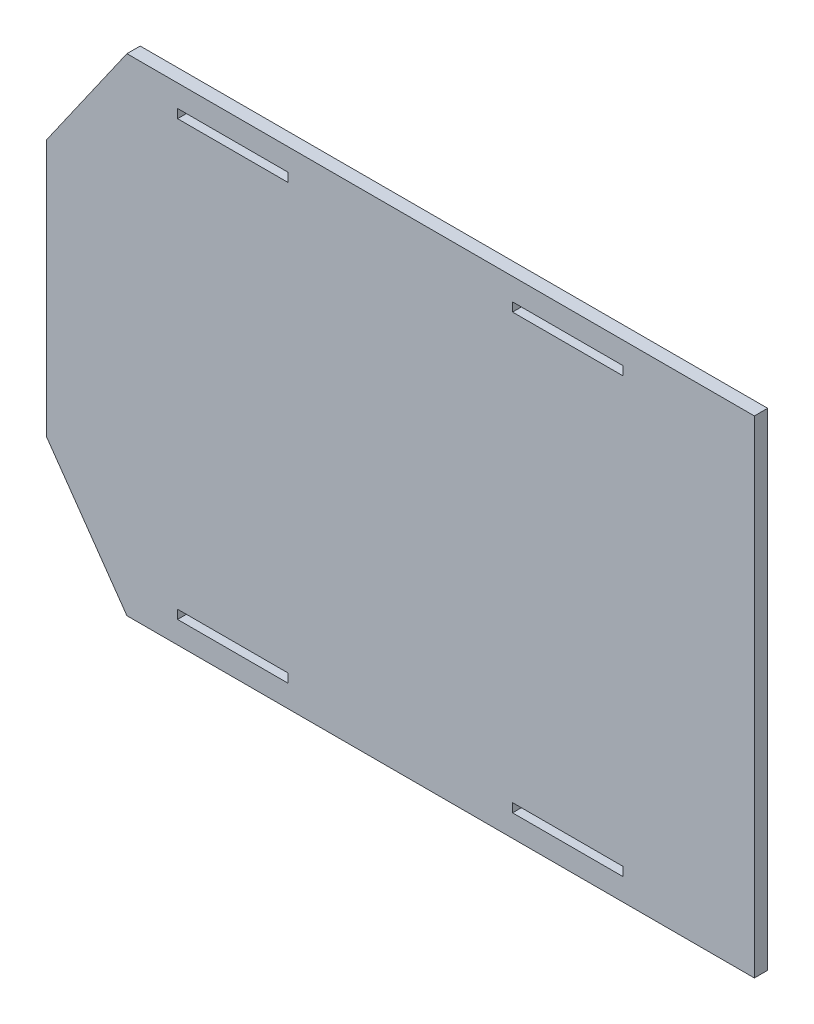
SolidWorks part; units mm, degrees
ref_plane "Ebene vorne" through (0, 0, 0) normal (0, 0, 1) x (1, 0, 0)
ref_plane "Ebene oben" through (0, 0, 0) normal (0, 1, 0) x (1, 0, 0)
ref_plane "Ebene rechts" through (0, 0, 0) normal (1, 0, 0) x (0, 0, -1)
sketch "Skizze1" plane through (0, 0, 0) normal (0, 0, 1) x (1, 0, 0)
  line L1 (0, 0) -> (320, 0)
  line L2 (0, 0) -> (0, 220)
  line L3 (0, 220) -> (320, 220)
  line L4 (320, 0) -> (320, 220)
  dimension "D1" = 220
  dimension "D2" = 320
extrude "Aufsatz-Linear austragen1" add sketch "Skizze1" along normal blind 6
sketch "Skizze2" plane through (0, 0, 6) normal (0, 0, 1) x (1, 0, 0)
  line L0 (0, 110) -> (508.8137, 110) construction
  line L1 (0, 220) -> (0, 0) construction
  line L2 (160, -38.5334) -> (160, 341.9392) construction
  line L3 (320, 0) -> (320, 220) construction
  line L4 (109.3, 206) -> (109.3, 210) construction
  line L5 (59.3, 210) -> (109.3, 210)
  line L6 (59.3, 210) -> (59.3, 206)
  line L7 (59.3, 206) -> (109.3, 206)
  line L8 (109.3, 210) -> (109.3, 206)
  dimension "D1" = 50
  dimension "D2" = 4
  dimension "D4" = 96
extrude "Schnitt-Linear austragen1" cut sketch "Skizze2" against normal up to next (6 mm away)
ref_plane "Ebene1" through (160, 0, 0) normal (1, 0, 0) x (0, 0, -1)
ref_plane "Ebene2" through (0, 110, 0) normal (0, 1, 0) x (1, 0, 0)
mirror "Spiegeln1" about plane through (160, 0, 0) normal (1, 0, 0) of "Schnitt-Linear austragen1"
mirror "Spiegeln2" about plane through (0, 110, 0) normal (0, 1, 0) of "Spiegeln1", "Schnitt-Linear austragen1"
sketch "Skizze3" plane through (0, 0, 6) normal (0, 0, 1) x (1, 0, 0)
  line L0 (0, 52) -> (36.4108, 0)
  line L1 (0, 220) -> (0, 0) construction
  line L2 (0, 0) -> (320, 0) construction
  line L3 (36.4108, 0) -> (0, 0)
  line L4 (0, 0) -> (0, 52)
  dimension "D1" = 55
  dimension "D2" = 52
extrude "Schnitt-Linear austragen2" cut sketch "Skizze3" against normal up to next (6 mm away)
mirror "Spiegeln3" about plane through (0, 110, 0) normal (0, 1, 0) of "Schnitt-Linear austragen2"
